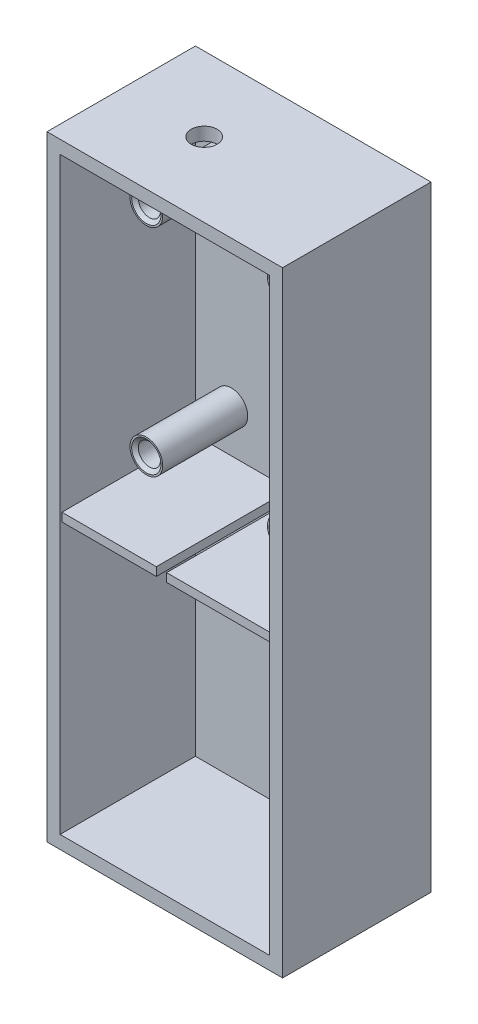
SolidWorks part; units mm, degrees
ref_plane "Front Plane" through (0, 0, 0) normal (0, 0, 1) x (1, 0, 0)
ref_plane "Top Plane" through (0, 0, 0) normal (0, 1, 0) x (1, 0, 0)
ref_plane "Right Plane" through (0, 0, 0) normal (1, 0, 0) x (0, 0, -1)
sketch "Sketch1" plane through (0, 0, 0) normal (0, 0, 1) x (1, 0, 0)
  line L0 (22.86, 59.69) -> (-22.86, -59.69) construction
  line L1 (-22.86, 59.69) -> (22.86, 59.69)
  line L2 (-22.86, 59.69) -> (-22.86, -59.69)
  line L3 (-22.86, -59.69) -> (22.86, -59.69)
  line L4 (22.86, 59.69) -> (22.86, -59.69)
  point P4 (0, 0)
  point P5 (0, 0)
  dimension "D1" = 119.38
  dimension "D2" = 45.72
extrude "Boss-Extrude1" add sketch "Sketch1" along normal mid plane 28.8071 contours L1 L4 L3 L2
shell "Shell3" thickness 2.54
sketch "Sketch4" plane through (0, 0, -11.8636) normal (0, 0, 1) x (1, 0, 0)
  line L0 (-13.335, 46.99) -> (13.335, 46.99) construction
  line L1 (-20.32, 57.15) -> (-20.32, -57.15) construction
  line L2 (13.335, 46.99) -> (13.335, 5.08) construction
  line L3 (-20.32, -57.15) -> (20.32, -57.15) construction
  line L4 (13.335, 5.08) -> (-13.335, 5.08) construction
  line L5 (-13.335, 46.99) -> (-13.335, 5.08) construction
  circle A0 centre (-13.335, 46.99) radius 3.175
  circle A2 centre (13.335, 46.99) radius 3.175
  circle A3 centre (13.335, 5.08) radius 3.175
  circle A4 centre (-13.335, 5.08) radius 3.175
  dimension "D1" = 6.35
  dimension "D2" = 26.67
  dimension "D4" = 41.91
  dimension "D6" = 62.23
  dimension "D7" = 62.23
  dimension "D8" = 6.35
  dimension "D9" = 6.35
  dimension "D10" = 6.35
  dimension "D3" = 6.985
  dimension "D5" = 41.91
extrude "Boss-Extrude2" add sketch "Sketch4" along normal blind 16.51
sketch "Sketch7" plane through (0, 0, 4.6464) normal (0, 0, 1) x (1, 0, 0)
  point P0 (-13.335, 46.99)
  point P1 (13.335, 46.99)
  point P3 (13.335, 5.08)
  point P5 (-13.335, 5.08)
  point P7 (0, 0)
hole_wizard "#8 (0.199) Diameter Hole1" positions "Sketch12" profile "Sketch13" hole size "#8" standard "ANSI Inch" end condition up to next
sketch "Sketch12" plane through (0, 59.69, 0) normal (0, 1, 0) x (1, 0, 0)
  point P0 (-6.7619, 0)
  point P2 (-42.2856, -5.5596)
sketch "Sketch13" plane through (-6.7619, 59.69, 0) normal (1, 0, 0) x (0, 0, 1)
  line L0 (0, 0) -> (0, 2.54)
  line L1 (0, 2.54) -> (2.5273, 2.54)
  line L2 (2.5273, 2.54) -> (2.5273, 0)
  line L5 (2.5273, 0) -> (0, 0)
  line L11 (0, -6.35) -> (0, 107.95) construction
  dimension "Thru Hole Dia." = 5.0546
  dimension "Thru Hole Depth" = 2.54
sketch "Sketch14" plane through (0, 59.69, 0) normal (0, 1, 0) x (1, 0, 0)
  line L1 (3.874, 3.2905) -> (9.8938, 3.2905)
  line L2 (3.874, 3.2905) -> (3.874, -2.7293)
  line L3 (3.874, -2.7293) -> (9.8938, -2.7293)
  line L4 (9.8938, 3.2905) -> (9.8938, -2.7293)
  dimension "D1" = 6.0198
  dimension "D2" = 6.0198
sketch "Sketch19" plane through (0, 0, -11.8636) normal (0, 0, 1) x (1, 0, 0)
  line L0 (-20.32, 57.15) -> (-20.32, -57.15) construction
  line L1 (-20.32, -3.1706) -> (20.32, -3.1706)
  line L2 (-20.32, -3.1706) -> (-20.32, -4.8133)
  line L3 (-20.32, -4.8133) -> (20.32, -4.8133)
  line L4 (20.32, -3.1706) -> (20.32, -4.8133)
  line L5 (20.32, 57.15) -> (20.32, -57.15) construction
extrude "Boss-Extrude3" add sketch "Sketch19" along normal blind 25.908
sketch "Sketch23" plane through (0, -4.8133, 0) normal (0, -1, 0) x (1, 0, 0)
  line L0 (-20.32, 14.0444) -> (20.32, 14.0444) construction
  line L1 (-2.0022, 14.0444) -> (0, 14.0444)
  line L2 (-2.0022, 14.0444) -> (-2.0022, -11.8636)
  line L3 (-2.0022, -11.8636) -> (0, -11.8636)
  line L4 (0, 14.0444) -> (0, -11.8636)
  line L5 (-20.32, -11.8636) -> (20.32, -11.8636) construction
extrude "Cut-Extrude2" cut sketch "Sketch23" against normal blind 15.748
hole_wizard "#4 (0.209) Diameter Hole1" positions "Sketch25" profile "Sketch26" hole size "#4" standard "ANSI Inch"
sketch "Sketch25" plane through (0, 0, 4.6464) normal (0, 0, 1) x (1, 0, 0)
  point P0 (-13.335, 5.08)
  point P3 (-13.335, 46.99)
  point P6 (13.335, 5.08)
  point P9 (13.335, 46.99)
sketch "Sketch26" plane through (-13.335, 5.08, 4.6464) normal (1, 0, 0) x (0, -1, 0)
  line L0 (0, 0) -> (0, 14.7516)
  line L1 (0, 14.7516) -> (2.1463, 13.462)
  line L2 (2.1463, 13.462) -> (2.1463, 0.5861)
  line L3 (2.1463, 0.5861) -> (2.8448, 0)
  line L5 (2.8448, 0) -> (0, 0)
  line L6 (-2.1463, 0.5861) -> (-2.8448, 0) construction
  line L10 (0, 14.7516) -> (-2.1463, 13.462) construction
  line L11 (0, -6.35) -> (0, 107.95) construction
  dimension "Hole Dia." = 4.2926
  dimension "Hole Depth" = 13.462
  dimension "Near C'Sink Dia." = 5.6896
  dimension "Near C'Sink Angle" = 100
  dimension "Drill Angle" = 118
